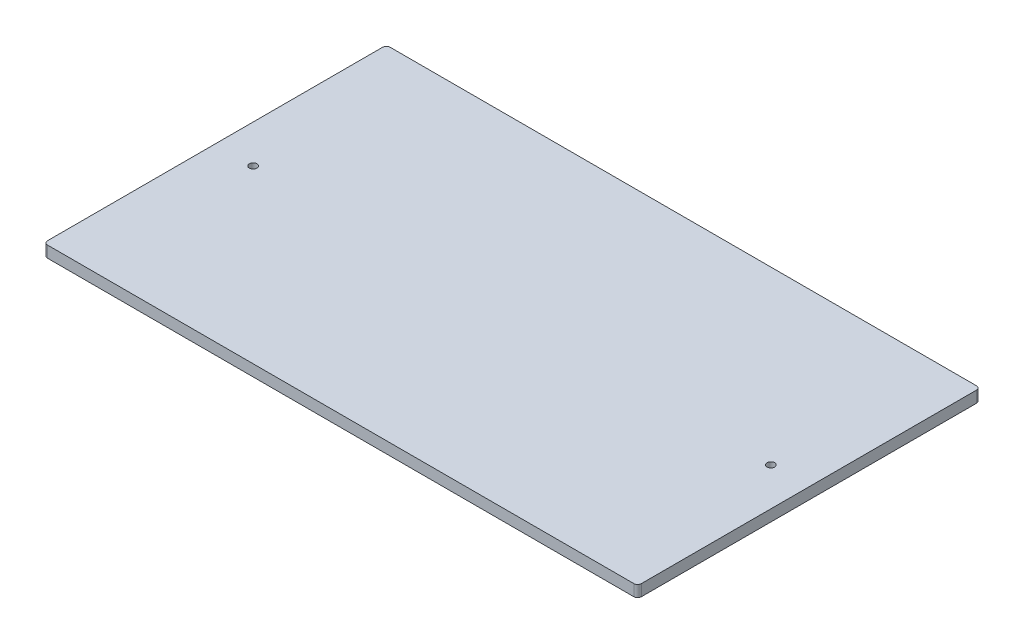
SolidWorks part; units mm, degrees
ref_plane "Front Plane" through (0, 0, 0) normal (0, 0, 1) x (1, 0, 0)
ref_plane "Top Plane" through (0, 0, 0) normal (0, 1, 0) x (1, 0, 0)
ref_plane "Right Plane" through (0, 0, 0) normal (1, 0, 0) x (0, 0, -1)
sketch "Sketch1" plane through (0, 0, 0) normal (0, 1, 0) x (1, 0, 0)
  line L1 (0, 0) -> (156, 0)
  line L2 (0, 0) -> (0, 90)
  line L3 (0, 90) -> (156, 90)
  line L4 (156, 0) -> (156, 90)
  dimension "D1" = 90
  dimension "D2" = 156
extrude "Boss-Extrude1" add sketch "Sketch1" along normal blind 3
fillet "Fillet1" radius 1 4 edges at (0, 1.5, -90) (156, 1.5, -90) (156, 1.5, 0) (0, 1.5, 0)
sketch "Sketch2" plane through (0, 3, 0) normal (0, 1, 0) x (1, 0, 0)
  line L0 (1, 0) -> (155, 0) construction
  line L1 (156, 1) -> (156, 89) construction
  line L2 (0, 89) -> (0, 1) construction
  circle A0 centre (146, 45) radius 1
  circle A1 centre (10, 45) radius 1
  point P8 (3.6297, 45)
  point P9 (0, 0)
  dimension "D1" = 2
  dimension "D2" = 45
  dimension "D3" = 10
  dimension "D4" = 10
extrude "Cut-Extrude1" cut sketch "Sketch2" against normal through all
